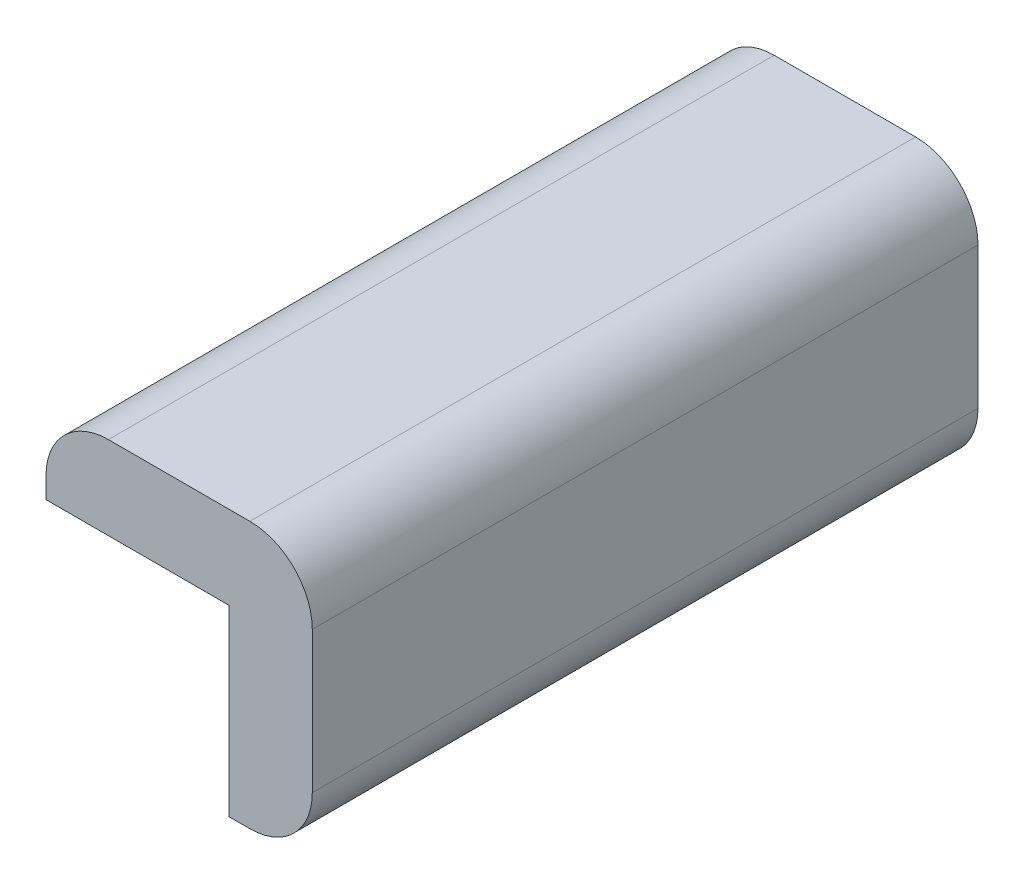
SolidWorks part; units mm, degrees
ref_plane "Front Plane" through (0, 0, 0) normal (0, 0, 1) x (1, 0, 0)
ref_plane "Top Plane" through (0, 0, 0) normal (0, 1, 0) x (1, 0, 0)
ref_plane "Right Plane" through (0, 0, 0) normal (1, 0, 0) x (0, 0, -1)
ref_plane "Plane1" through (0, 0, 80) normal (0, 0, 1) x (1, 0, 0)
sketch "Sketch1" plane through (0, 0, 80) normal (0, 0, 1) x (1, 0, 0)
  line L0 (-22, 24.5) -> (-22, 22)
  line L1 (-22, 22) -> (0, 22)
  line L2 (0, 22) -> (0, 0)
  line L3 (0, 0) -> (2.5, 0)
  line L4 (10, 7.5) -> (10, 24.5)
  line L5 (2.5, 32) -> (-14.5, 32)
  arc A0 (2.5, 0) -> (10, 7.5) centre (2.5, 7.5) ccw
  arc A1 (10, 24.5) -> (2.5, 32) centre (2.5, 24.5) ccw
  arc A2 (-14.5, 32) -> (-22, 24.5) centre (-14.5, 24.5) ccw
extrude "Boss-Extrude1" add sketch "Sketch1" against normal blind 80
